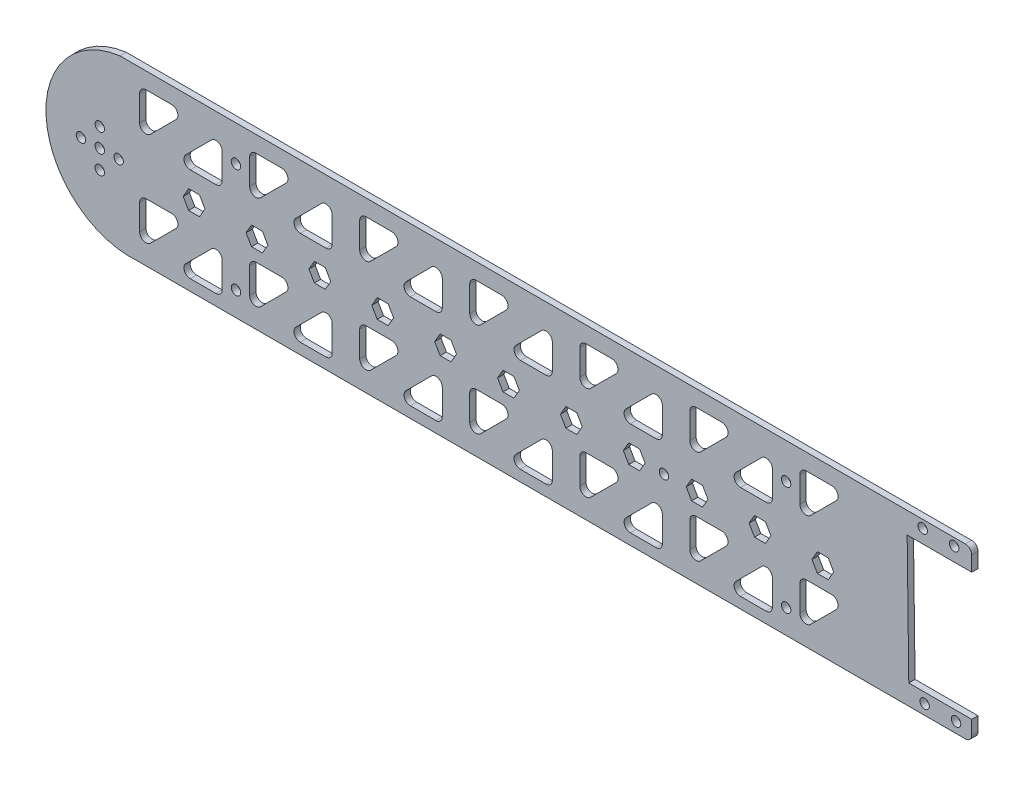
SolidWorks part; units mm, degrees
ref_plane "Ön Düzlem" through (0, 0, 0) normal (0, 0, 1) x (1, 0, 0)
ref_plane "Üst Düzlem" through (0, 0, 0) normal (0, 1, 0) x (1, 0, 0)
ref_plane "Sağ Düzlem" through (0, 0, 0) normal (1, 0, 0) x (0, 0, -1)
sketch "Çizim1" plane through (0, 0, 0) normal (0, 0, 1) x (1, 0, 0)
  line L0 (0, 34.9435) -> (0, -25.0192) construction
  line L1 (-123.6821, 28.6804) -> (123.6821, 28.6804)
  line L3 (-118.1627, -25.0192) -> (118.1627, -25.0192)
  line L5 (-150.2336, 30.0467) -> (150, -30) construction
  line L6 (123.6821, 28.6804) -> (137.2391, 28.6804)
  line L7 (-0.1168, 0.0234) -> (-130.1063, 0.0234) construction
  line L8 (-130.1063, 6.0234) -> (-130.1063, -6.1534) construction
  line L9 (-18.3887, -2.9789) -> (-16.6527, 0.0189)
  line L10 (1.6113, -2.9789) -> (3.3473, 0.0189)
  line L11 (3.3473, 0.0189) -> (1.6191, 3.0211)
  line L12 (1.6191, 3.0211) -> (-1.845, 3.0256)
  line L13 (-1.845, 3.0256) -> (-3.5809, 0.0279)
  line L14 (-3.5809, 0.0279) -> (-1.8528, -2.9744)
  line L15 (-1.8528, -2.9744) -> (1.6113, -2.9789)
  line L16 (-16.6527, 0.0189) -> (-18.3809, 3.0211)
  line L17 (-18.3809, 3.0211) -> (-21.845, 3.0256)
  line L18 (-21.845, 3.0256) -> (-23.5809, 0.0279)
  line L19 (-23.5809, 0.0279) -> (-21.8528, -2.9744)
  line L20 (-21.8528, -2.9744) -> (-18.3887, -2.9789)
  line L21 (-38.3887, -2.9789) -> (-36.6527, 0.0189)
  line L22 (-36.6527, 0.0189) -> (-38.3809, 3.0211)
  line L23 (-38.3809, 3.0211) -> (-41.845, 3.0256)
  line L24 (-41.845, 3.0256) -> (-43.5809, 0.0279)
  line L25 (-43.5809, 0.0279) -> (-41.8528, -2.9744)
  line L26 (-41.8528, -2.9744) -> (-38.3887, -2.9789)
  line L27 (-58.3887, -2.9789) -> (-56.6527, 0.0189)
  line L28 (-56.6527, 0.0189) -> (-58.3809, 3.0211)
  line L29 (-58.3809, 3.0211) -> (-61.845, 3.0256)
  line L30 (-61.845, 3.0256) -> (-63.5809, 0.0279)
  line L31 (-63.5809, 0.0279) -> (-61.8528, -2.9744)
  line L32 (-61.8528, -2.9744) -> (-58.3887, -2.9789)
  line L33 (-78.3887, -2.9789) -> (-76.6527, 0.0189)
  line L34 (-76.6527, 0.0189) -> (-78.3809, 3.0211)
  line L35 (-78.3809, 3.0211) -> (-81.845, 3.0256)
  line L36 (-81.845, 3.0256) -> (-83.5809, 0.0279)
  line L37 (-83.5809, 0.0279) -> (-81.8528, -2.9744)
  line L38 (-81.8528, -2.9744) -> (-78.3887, -2.9789)
  line L39 (-98.3887, -2.9789) -> (-96.6527, 0.0189)
  line L40 (-96.6527, 0.0189) -> (-98.3809, 3.0211)
  line L41 (-98.3809, 3.0211) -> (-101.845, 3.0256)
  line L42 (-101.845, 3.0256) -> (-103.5809, 0.0279)
  line L43 (-103.5809, 0.0279) -> (-101.8528, -2.9744)
  line L44 (-101.8528, -2.9744) -> (-98.3887, -2.9789)
  line L45 (21.6113, -2.9789) -> (23.3473, 0.0189)
  line L46 (18.1472, -2.9744) -> (21.6113, -2.9789)
  line L47 (16.4191, 0.0279) -> (18.1472, -2.9744)
  line L48 (18.155, 3.0256) -> (16.4191, 0.0279)
  line L49 (21.6191, 3.0211) -> (18.155, 3.0256)
  line L50 (23.3473, 0.0189) -> (21.6191, 3.0211)
  line L51 (41.6113, -2.9789) -> (43.3473, 0.0189)
  line L52 (38.1472, -2.9744) -> (41.6113, -2.9789)
  line L53 (36.4191, 0.0279) -> (38.1472, -2.9744)
  line L54 (38.155, 3.0256) -> (36.4191, 0.0279)
  line L55 (41.6191, 3.0211) -> (38.155, 3.0256)
  line L56 (43.3473, 0.0189) -> (41.6191, 3.0211)
  line L57 (61.6113, -2.9789) -> (63.3473, 0.0189)
  line L58 (58.1472, -2.9744) -> (61.6113, -2.9789)
  line L59 (56.4191, 0.0279) -> (58.1472, -2.9744)
  line L60 (58.155, 3.0256) -> (56.4191, 0.0279)
  line L61 (61.6191, 3.0211) -> (58.155, 3.0256)
  line L62 (63.3473, 0.0189) -> (61.6191, 3.0211)
  line L63 (81.6113, -2.9789) -> (83.3473, 0.0189)
  line L64 (78.1472, -2.9744) -> (81.6113, -2.9789)
  line L65 (76.4191, 0.0279) -> (78.1472, -2.9744)
  line L66 (78.155, 3.0256) -> (76.4191, 0.0279)
  line L67 (81.6191, 3.0211) -> (78.155, 3.0256)
  line L68 (83.3473, 0.0189) -> (81.6191, 3.0211)
  line L69 (101.6113, -2.9789) -> (103.3473, 0.0189)
  line L70 (98.1472, -2.9744) -> (101.6113, -2.9789)
  line L71 (96.4191, 0.0279) -> (98.1472, -2.9744)
  line L72 (98.155, 3.0256) -> (96.4191, 0.0279)
  line L73 (101.6191, 3.0211) -> (98.155, 3.0256)
  line L74 (103.3473, 0.0189) -> (101.6191, 3.0211)
  line L75 (-117.433, 15.462) -> (117.433, 15.462) construction
  line L76 (-117.433, 21.4866) -> (-117.433, 13.315)
  line L77 (-115.433, 23.4866) -> (-107.2614, 23.4866)
  line L78 (-105.8472, 20.0724) -> (-114.0187, 11.9008)
  line L79 (-94.5849, 20.0724) -> (-102.7565, 11.9008)
  line L80 (-101.3423, 8.4866) -> (-93.1707, 8.4866)
  line L81 (-91.1707, 10.4866) -> (-91.1707, 18.6582)
  line L82 (-82.433, 21.4866) -> (-82.433, 13.315)
  line L83 (-80.433, 23.4866) -> (-72.2614, 23.4866)
  line L84 (-70.8472, 20.0724) -> (-79.0187, 11.9008)
  line L85 (-59.5849, 20.0724) -> (-67.7565, 11.9008)
  line L86 (-66.3423, 8.4866) -> (-58.1707, 8.4866)
  line L87 (-56.1707, 10.4866) -> (-56.1707, 18.6582)
  line L88 (-47.433, 21.4866) -> (-47.433, 13.315)
  line L89 (-45.433, 23.4866) -> (-37.2614, 23.4866)
  line L90 (-35.8472, 20.0724) -> (-44.0187, 11.9008)
  line L91 (-24.5849, 20.0724) -> (-32.7565, 11.9008)
  line L92 (-31.3423, 8.4866) -> (-23.1707, 8.4866)
  line L93 (-21.1707, 10.4866) -> (-21.1707, 18.6582)
  line L94 (-12.433, 21.4866) -> (-12.433, 13.315)
  line L95 (-10.433, 23.4866) -> (-2.2614, 23.4866)
  line L96 (-0.8472, 20.0724) -> (-9.0187, 11.9008)
  line L97 (10.4151, 20.0724) -> (2.2435, 11.9008)
  line L98 (3.6577, 8.4866) -> (11.8293, 8.4866)
  line L99 (13.8293, 10.4866) -> (13.8293, 18.6582)
  line L100 (22.567, 21.4866) -> (22.567, 13.315)
  line L101 (24.567, 23.4866) -> (32.7386, 23.4866)
  line L102 (34.1528, 20.0724) -> (25.9813, 11.9008)
  line L103 (45.4151, 20.0724) -> (37.2435, 11.9008)
  line L104 (38.6577, 8.4866) -> (46.8293, 8.4866)
  line L105 (48.8293, 10.4866) -> (48.8293, 18.6582)
  line L106 (57.567, 21.4866) -> (57.567, 13.315)
  line L107 (59.567, 23.4866) -> (67.7386, 23.4866)
  line L108 (69.1528, 20.0724) -> (60.9813, 11.9008)
  line L109 (80.4151, 20.0724) -> (72.2435, 11.9008)
  line L110 (73.6577, 8.4866) -> (81.8293, 8.4866)
  line L111 (83.8293, 10.4866) -> (83.8293, 18.6582)
  line L112 (92.567, 21.4866) -> (92.567, 13.315)
  line L113 (94.567, 23.4866) -> (102.7386, 23.4866)
  line L114 (104.1528, 20.0724) -> (95.9813, 11.9008)
  line L118 (-82.433, -8.5134) -> (-82.433, -16.685)
  line L119 (-80.433, -6.5134) -> (-72.2614, -6.5134)
  line L120 (-70.8472, -9.9276) -> (-79.0187, -18.0992)
  line L121 (-59.5849, -9.9276) -> (-67.7565, -18.0992)
  line L122 (-66.3423, -21.5134) -> (-58.1707, -21.5134)
  line L123 (-56.1707, -19.5134) -> (-56.1707, -11.3418)
  line L124 (-47.433, -8.5134) -> (-47.433, -16.685)
  line L125 (-45.433, -6.5134) -> (-37.2614, -6.5134)
  line L126 (-35.8472, -9.9276) -> (-44.0187, -18.0992)
  line L127 (-24.5849, -9.9276) -> (-32.7565, -18.0992)
  line L128 (-31.3423, -21.5134) -> (-23.1707, -21.5134)
  line L129 (-21.1707, -19.5134) -> (-21.1707, -11.3418)
  line L130 (-12.433, -8.5134) -> (-12.433, -16.685)
  line L131 (-10.433, -6.5134) -> (-2.2614, -6.5134)
  line L132 (-0.8472, -9.9276) -> (-9.0187, -18.0992)
  line L133 (10.4151, -9.9276) -> (2.2435, -18.0992)
  line L134 (3.6577, -21.5134) -> (11.8293, -21.5134)
  line L135 (13.8293, -19.5134) -> (13.8293, -11.3418)
  line L136 (22.567, -8.5134) -> (22.567, -16.685)
  line L137 (24.567, -6.5134) -> (32.7386, -6.5134)
  line L138 (34.1528, -9.9276) -> (25.9813, -18.0992)
  line L139 (45.4151, -9.9276) -> (37.2435, -18.0992)
  line L140 (38.6577, -21.5134) -> (46.8293, -21.5134)
  line L141 (48.8293, -19.5134) -> (48.8293, -11.3418)
  line L142 (57.567, -8.5134) -> (57.567, -16.685)
  line L143 (59.567, -6.5134) -> (67.7386, -6.5134)
  line L144 (69.1528, -9.9276) -> (60.9813, -18.0992)
  line L145 (80.4151, -9.9276) -> (72.2435, -18.0992)
  line L146 (73.6577, -21.5134) -> (81.8293, -21.5134)
  line L147 (83.8293, -19.5134) -> (83.8293, -11.3418)
  line L148 (92.567, -8.5134) -> (92.567, -16.685)
  line L149 (94.567, -6.5134) -> (102.7386, -6.5134)
  line L150 (104.1528, -9.9276) -> (95.9813, -18.0992)
  line L154 (-117.433, -8.5134) -> (-117.433, -16.685)
  line L155 (-115.433, -6.5134) -> (-107.2614, -6.5134)
  line L156 (-105.8472, -9.9276) -> (-114.0187, -18.0992)
  line L157 (-94.5849, -9.9276) -> (-102.7565, -18.0992)
  line L158 (-101.3423, -21.5134) -> (-93.1707, -21.5134)
  line L159 (-91.1707, -19.5134) -> (-91.1707, -11.3418)
  line L160 (-0.1168, 0.0234) -> (147.2391, 1.9008) construction
  line L161 (147.2391, 18.6804) -> (147.2391, -15.0192)
  line L168 (108.6577, 8.4866) -> (116.8293, 8.4866) [skipped]
  line L169 (118.8293, 10.4866) -> (118.8293, 18.6582) [skipped]
  line L170 (118.8293, -19.5134) -> (118.8293, -11.3418) [skipped]
  line L171 (115.4151, -9.9276) -> (107.2435, -18.0992) [skipped]
  line L172 (108.6577, -21.5134) -> (116.8293, -21.5134) [skipped]
  line L173 (115.4151, 20.0724) -> (110.8046, 15.462) [skipped]
  line L176 (110.2391, 21.9008) -> (130.2391, -18.0992) construction
  line L177 (110.2391, -18.0992) -> (130.2391, 21.9008) construction
  line L178 (137.2391, -25.0192) -> (118.1627, -25.0192)
  line L179 (146.7064, 21.9008) -> (126.7064, 21.9008)
  line L180 (127.2226, -18.6158) -> (146.57, -18.6158)
  line L181 (126.7064, 21.9008) -> (127.2226, -18.6158)
  line L182 (147.2391, -15.0192) -> (147.2391, -23.0192)
  line L183 (145.2391, -25.0192) -> (137.2391, -25.0192)
  line L184 (137.2391, 28.6804) -> (145.2391, 28.6804)
  line L185 (147.2391, 26.6804) -> (147.2391, 18.6804)
  line L186 (146.7064, 21.9008) -> (147.2391, 21.9008)
  line L187 (146.57, -18.6158) -> (147.2391, -18.6158)
  arc A0 (-123.6821, 28.6804) -> (-118.1627, -25.0192) centre (-120.2391, 1.9008) ccw
  circle A2 centre (-130.1063, 0.0234) radius 10
  circle A3 centre (-130.1063, 6.0234) radius 1.5
  circle A4 centre (-130.1063, -5.9766) radius 1.5
  circle A5 centre (-136.1063, 0.0234) radius 1.5
  circle A6 centre (-130.1063, 6.0234) radius 1.5
  circle A7 centre (-124.1063, 0.0234) radius 1.5
  circle A8 centre (-130.1063, 0.0234) radius 1.5
  circle A15 centre (-0.1168, 0.0234) radius 3 construction
  arc A16 (-101.3423, 8.4866) -> (-102.7565, 11.9008) centre (-101.3423, 10.4866) cw
  arc A17 (-93.1707, 8.4866) -> (-91.1707, 10.4866) centre (-93.1707, 10.4866) ccw
  arc A18 (-91.1707, 18.6582) -> (-94.5849, 20.0724) centre (-93.1707, 18.6582) ccw
  arc A19 (-114.0187, 11.9008) -> (-117.433, 13.315) centre (-115.433, 13.315) cw
  arc A20 (-107.2614, 23.4866) -> (-105.8472, 20.0724) centre (-107.2614, 21.4866) cw
  arc A21 (-117.433, 21.4866) -> (-115.433, 23.4866) centre (-115.433, 21.4866) cw
  arc A22 (-72.2614, 23.4866) -> (-70.8472, 20.0724) centre (-72.2614, 21.4866) cw
  arc A23 (-82.433, 21.4866) -> (-80.433, 23.4866) centre (-80.433, 21.4866) cw
  arc A24 (-79.0187, 11.9008) -> (-82.433, 13.315) centre (-80.433, 13.315) cw
  arc A25 (-66.3423, 8.4866) -> (-67.7565, 11.9008) centre (-66.3423, 10.4866) cw
  arc A26 (-58.1707, 8.4866) -> (-56.1707, 10.4866) centre (-58.1707, 10.4866) ccw
  arc A27 (-56.1707, 18.6582) -> (-59.5849, 20.0724) centre (-58.1707, 18.6582) ccw
  arc A28 (-37.2614, 23.4866) -> (-35.8472, 20.0724) centre (-37.2614, 21.4866) cw
  arc A29 (-47.433, 21.4866) -> (-45.433, 23.4866) centre (-45.433, 21.4866) cw
  arc A30 (-44.0187, 11.9008) -> (-47.433, 13.315) centre (-45.433, 13.315) cw
  arc A31 (-31.3423, 8.4866) -> (-32.7565, 11.9008) centre (-31.3423, 10.4866) cw
  arc A32 (-23.1707, 8.4866) -> (-21.1707, 10.4866) centre (-23.1707, 10.4866) ccw
  arc A33 (-21.1707, 18.6582) -> (-24.5849, 20.0724) centre (-23.1707, 18.6582) ccw
  arc A34 (-2.2614, 23.4866) -> (-0.8472, 20.0724) centre (-2.2614, 21.4866) cw
  arc A35 (-12.433, 21.4866) -> (-10.433, 23.4866) centre (-10.433, 21.4866) cw
  arc A36 (-9.0187, 11.9008) -> (-12.433, 13.315) centre (-10.433, 13.315) cw
  arc A37 (3.6577, 8.4866) -> (2.2435, 11.9008) centre (3.6577, 10.4866) cw
  arc A38 (11.8293, 8.4866) -> (13.8293, 10.4866) centre (11.8293, 10.4866) ccw
  arc A39 (13.8293, 18.6582) -> (10.4151, 20.0724) centre (11.8293, 18.6582) ccw
  arc A40 (32.7386, 23.4866) -> (34.1528, 20.0724) centre (32.7386, 21.4866) cw
  arc A41 (22.567, 21.4866) -> (24.567, 23.4866) centre (24.567, 21.4866) cw
  arc A42 (25.9813, 11.9008) -> (22.567, 13.315) centre (24.567, 13.315) cw
  arc A43 (38.6577, 8.4866) -> (37.2435, 11.9008) centre (38.6577, 10.4866) cw
  arc A44 (46.8293, 8.4866) -> (48.8293, 10.4866) centre (46.8293, 10.4866) ccw
  arc A45 (48.8293, 18.6582) -> (45.4151, 20.0724) centre (46.8293, 18.6582) ccw
  arc A46 (67.7386, 23.4866) -> (69.1528, 20.0724) centre (67.7386, 21.4866) cw
  arc A47 (57.567, 21.4866) -> (59.567, 23.4866) centre (59.567, 21.4866) cw
  arc A48 (60.9813, 11.9008) -> (57.567, 13.315) centre (59.567, 13.315) cw
  arc A49 (73.6577, 8.4866) -> (72.2435, 11.9008) centre (73.6577, 10.4866) cw
  arc A50 (81.8293, 8.4866) -> (83.8293, 10.4866) centre (81.8293, 10.4866) ccw
  arc A51 (83.8293, 18.6582) -> (80.4151, 20.0724) centre (81.8293, 18.6582) ccw
  arc A52 (102.7386, 23.4866) -> (104.1528, 20.0724) centre (102.7386, 21.4866) cw
  arc A53 (92.567, 21.4866) -> (94.567, 23.4866) centre (94.567, 21.4866) cw
  arc A54 (95.9813, 11.9008) -> (92.567, 13.315) centre (94.567, 13.315) cw
  arc A58 (-72.2614, -6.5134) -> (-70.8472, -9.9276) centre (-72.2614, -8.5134) cw
  arc A59 (-82.433, -8.5134) -> (-80.433, -6.5134) centre (-80.433, -8.5134) cw
  arc A60 (-79.0187, -18.0992) -> (-82.433, -16.685) centre (-80.433, -16.685) cw
  arc A61 (-66.3423, -21.5134) -> (-67.7565, -18.0992) centre (-66.3423, -19.5134) cw
  arc A62 (-58.1707, -21.5134) -> (-56.1707, -19.5134) centre (-58.1707, -19.5134) ccw
  arc A63 (-56.1707, -11.3418) -> (-59.5849, -9.9276) centre (-58.1707, -11.3418) ccw
  arc A64 (-37.2614, -6.5134) -> (-35.8472, -9.9276) centre (-37.2614, -8.5134) cw
  arc A65 (-47.433, -8.5134) -> (-45.433, -6.5134) centre (-45.433, -8.5134) cw
  arc A66 (-44.0187, -18.0992) -> (-47.433, -16.685) centre (-45.433, -16.685) cw
  arc A67 (-31.3423, -21.5134) -> (-32.7565, -18.0992) centre (-31.3423, -19.5134) cw
  arc A68 (-23.1707, -21.5134) -> (-21.1707, -19.5134) centre (-23.1707, -19.5134) ccw
  arc A69 (-21.1707, -11.3418) -> (-24.5849, -9.9276) centre (-23.1707, -11.3418) ccw
  arc A70 (-2.2614, -6.5134) -> (-0.8472, -9.9276) centre (-2.2614, -8.5134) cw
  arc A71 (-12.433, -8.5134) -> (-10.433, -6.5134) centre (-10.433, -8.5134) cw
  arc A72 (-9.0187, -18.0992) -> (-12.433, -16.685) centre (-10.433, -16.685) cw
  arc A73 (3.6577, -21.5134) -> (2.2435, -18.0992) centre (3.6577, -19.5134) cw
  arc A74 (11.8293, -21.5134) -> (13.8293, -19.5134) centre (11.8293, -19.5134) ccw
  arc A75 (13.8293, -11.3418) -> (10.4151, -9.9276) centre (11.8293, -11.3418) ccw
  arc A76 (32.7386, -6.5134) -> (34.1528, -9.9276) centre (32.7386, -8.5134) cw
  arc A77 (22.567, -8.5134) -> (24.567, -6.5134) centre (24.567, -8.5134) cw
  arc A78 (25.9813, -18.0992) -> (22.567, -16.685) centre (24.567, -16.685) cw
  arc A79 (38.6577, -21.5134) -> (37.2435, -18.0992) centre (38.6577, -19.5134) cw
  arc A80 (46.8293, -21.5134) -> (48.8293, -19.5134) centre (46.8293, -19.5134) ccw
  arc A81 (48.8293, -11.3418) -> (45.4151, -9.9276) centre (46.8293, -11.3418) ccw
  arc A82 (67.7386, -6.5134) -> (69.1528, -9.9276) centre (67.7386, -8.5134) cw
  arc A83 (57.567, -8.5134) -> (59.567, -6.5134) centre (59.567, -8.5134) cw
  arc A84 (60.9813, -18.0992) -> (57.567, -16.685) centre (59.567, -16.685) cw
  arc A85 (73.6577, -21.5134) -> (72.2435, -18.0992) centre (73.6577, -19.5134) cw
  arc A86 (81.8293, -21.5134) -> (83.8293, -19.5134) centre (81.8293, -19.5134) ccw
  arc A87 (83.8293, -11.3418) -> (80.4151, -9.9276) centre (81.8293, -11.3418) ccw
  arc A88 (102.7386, -6.5134) -> (104.1528, -9.9276) centre (102.7386, -8.5134) cw
  arc A89 (92.567, -8.5134) -> (94.567, -6.5134) centre (94.567, -8.5134) cw
  arc A90 (95.9813, -18.0992) -> (92.567, -16.685) centre (94.567, -16.685) cw
  arc A94 (-107.2614, -6.5134) -> (-105.8472, -9.9276) centre (-107.2614, -8.5134) cw
  arc A95 (-117.433, -8.5134) -> (-115.433, -6.5134) centre (-115.433, -8.5134) cw
  arc A96 (-114.0187, -18.0992) -> (-117.433, -16.685) centre (-115.433, -16.685) cw
  arc A97 (-101.3423, -21.5134) -> (-102.7565, -18.0992) centre (-101.3423, -19.5134) cw
  arc A98 (-93.1707, -21.5134) -> (-91.1707, -19.5134) centre (-93.1707, -19.5134) ccw
  arc A99 (-91.1707, -11.3418) -> (-94.5849, -9.9276) centre (-93.1707, -11.3418) ccw
  arc A100 (116.8293, 8.4866) -> (118.8293, 10.4866) centre (116.8293, 10.4866) ccw [skipped]
  arc A101 (108.6577, 8.4866) -> (107.2435, 11.9008) centre (108.6577, 10.4866) cw [skipped]
  arc A102 (118.8293, -11.3418) -> (115.4151, -9.9276) centre (116.8293, -11.3418) ccw [skipped]
  arc A103 (108.6577, -21.5134) -> (107.2435, -18.0992) centre (108.6577, -19.5134) cw [skipped]
  arc A104 (118.8293, 18.6582) -> (115.4151, 20.0724) centre (116.8293, 18.6582) ccw [skipped]
  arc A105 (116.8293, -21.5134) -> (118.8293, -19.5134) centre (116.8293, -19.5134) ccw [skipped]
  arc A106 (147.2391, 18.6804) -> (146.7064, 21.9008) centre (137.2391, 18.6804) ccw
  arc A107 (147.2391, -15.0192) -> (146.57, -18.6158) centre (137.2391, -15.0192) cw
  arc A108 (145.2391, -25.0192) -> (147.2391, -23.0192) centre (145.2391, -23.0192) ccw
  arc A109 (147.2391, 26.6804) -> (145.2391, 28.6804) centre (145.2391, 26.6804) ccw
  circle A110 centre (131.652, 26.2022) radius 1.5
  circle A111 centre (141.6512, 26.3296) radius 1.5
  circle A112 centre (132.2635, -21.7939) radius 1.5
  circle A113 centre (142.2627, -21.6665) radius 1.5
  point P0 (0, 0)
  point P23 (120.3522, -2.2451)
  point P31 (-130.1063, 0.0234)
  point P124 (-117.433, 8.4866)
  point P127 (-102.433, 23.4866)
  point P130 (-117.433, 23.4866)
  dimension "D1" = 20
  dimension "D3" = 3
  dimension "D6" = 6
  dimension "D10" = 2
  dimension "D2" = 10
  dimension "D16" = 2
  dimension "D17" = 2
  dimension "D4" = 6
  dimension "D8" = 15
  dimension "D9" = 15
  dimension "D13" = 40
  dimension "D14" = 20
  dimension "D15" = 20
  dimension "D7" = 6
  dimension "D11" = 7
  dimension "D12" = 2
  dimension "D5" = 4
extrude "Yükseklik-Ekstrüzyon2" add sketch "Çizim1" along normal blind 2
sketch "Çizim9" plane through (0, 0, 0) normal (0, 0, -1) x (-1, 0, 0)
  line L0 (-92.567, 17.4008) -> (-83.8293, 17.4008) construction
  line L1 (-92.567, 21.4866) -> (-92.567, 13.315) construction
  line L2 (-83.8293, 10.4866) -> (-83.8293, 18.6582) construction
  line L3 (-88.1982, 17.4008) -> (-88.1982, -25.6798) construction
  line L4 (-96.4191, 0.0279) -> (-83.3473, 0.0189) construction
  line L5 (-1.8099, 9.7212) -> (-1.8099, -20.2788) construction
  line L6 (-96.4191, 0.0279) -> (96.6527, 0.0189) construction
  circle A0 centre (-88.1982, 17.4008) radius 1.5
  circle A1 centre (-88.2222, -17.3564) radius 1.5
  arc A2 (-3.6577, 8.4866) -> (-2.2435, 11.9008) centre (-3.6577, 10.4866) ccw construction
  arc A3 (-3.6577, -21.5134) -> (-2.2435, -18.0992) centre (-3.6577, -19.5134) ccw construction
  circle A4 centre (86.8018, 17.4008) radius 1.5
  circle A5 centre (86.7778, -17.3564) radius 1.5
  dimension "D1" = 2
extrude "Kes-Ekstrüzyon5" cut sketch "Çizim9" against normal blind 10
sketch "Çizim10" plane through (0, 0, 2) normal (0, 0, 1) x (1, 0, 0)
  circle A0 centre (49.3473, 0) radius 1.5
  dimension "D1" = 3
  dimension "D2" = 6
extrude "Kes-Ekstrüzyon7" cut sketch "Çizim10" against normal blind 10
